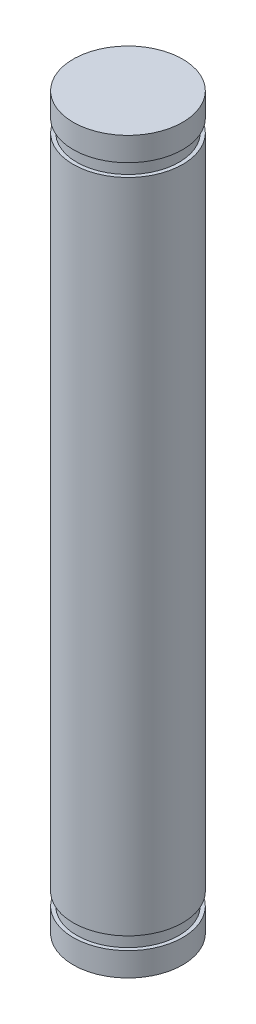
SolidWorks part; units mm, degrees
ref_plane "前视基准面" through (0, 0, 0) normal (0, 0, 1) x (1, 0, 0)
ref_plane "上视基准面" through (0, 0, 0) normal (0, 1, 0) x (1, 0, 0)
ref_plane "右视基准面" through (0, 0, 0) normal (1, 0, 0) x (0, 0, -1)
sketch "草图1" plane through (0, 0, 0) normal (0, 0, 1) x (1, 0, 0)
  line L0 (0, -20) -> (3, -20)
  line L1 (3, -20) -> (3, -18.7)
  line L2 (3, -18.7) -> (2.8, -18.7)
  line L3 (2.8, -18.7) -> (2.8, -18)
  line L4 (2.8, -18) -> (3, -18)
  line L5 (3, -18) -> (3, 18)
  line L6 (3, 18) -> (2.8, 18)
  line L7 (2.8, 18) -> (2.8, 18.7)
  line L8 (2.8, 18.7) -> (3, 18.7)
  line L9 (3, 18.7) -> (3, 20)
  line L10 (3, 20) -> (0, 20)
  line L11 (0, 20) -> (0, -20)
  point P13 (3.5137, -19.7)
  dimension "D2" = 3
  dimension "D3" = 1.3
  dimension "D4" = 0.2
  dimension "D5" = 0.7
  dimension "D6" = 36
  dimension "D7" = 0.7
  dimension "D8" = 1.3
revolve "旋转1" add sketch "草图1" angle 360 about L11
